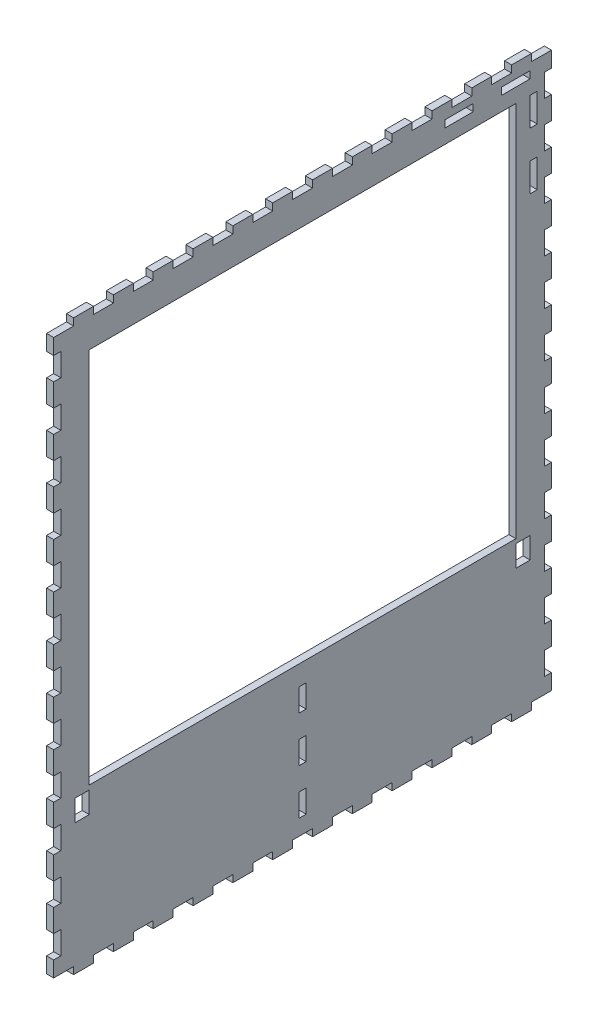
SolidWorks part; units mm, degrees
ref_plane "Plan de face" through (0, 0, 0) normal (0, 0, 1) x (1, 0, 0)
ref_plane "Plan de dessus" through (0, 0, 0) normal (0, 1, 0) x (1, 0, 0)
ref_plane "Plan de droite" through (0, 0, 0) normal (1, 0, 0) x (0, 0, -1)
sketch "Esquisse1" plane through (0, 0, 0) normal (1, 0, 0) x (0, 0, -1)
  line L1 (0, 0) -> (350, 0)
  line L2 (0, 0) -> (0, -400)
  line L3 (0, -400) -> (350, -400)
  line L4 (350, 0) -> (350, -400)
  dimension "D1" = 400
  dimension "D2" = 350
extrude "Boss.-Extru.1" add sketch "Esquisse1" along normal blind 5
sketch "Esquisse2" plane through (5, 0, 0) normal (1, 0, 0) x (0, 0, -1)
  line L0 (0, -400) -> (350, -400) construction
  line L1 (350, -400) -> (336, -400)
  line L2 (350, -400) -> (350, -395)
  line L3 (350, -395) -> (336, -395)
  line L4 (336, -400) -> (336, -395)
  dimension "D2" = 5
  dimension "D1" = 350
  dimension "D3" = 14
extrude "Enlèv. mat.-Extru.1" cut sketch "Esquisse2" against normal blind 5
ref_plane "Plan1" through (0, 0, -175) normal (0, 0, -1) x (-1, 0, 0)
ref_plane "Plan3" through (0, -200, 0) normal (0, -1, 0) x (-1, 0, 0)
pattern_linear "Répétition linéaire1" count 13 spacing 28 along (0, 0, 1) of "Enlèv. mat.-Extru.1"
mirror "Symétrie1" about plane through (0, -200, 0) normal (0, -1, 0) of "Répétition linéaire1", "Enlèv. mat.-Extru.1"
sketch "Esquisse3" plane through (5, 0, 0) normal (1, 0, 0) x (0, 0, -1)
  line L0 (350, -395) -> (350, -5) construction
  line L1 (350, -384) -> (345, -384)
  line L2 (350, -384) -> (350, -368)
  line L3 (350, -368) -> (345, -368)
  line L4 (345, -384) -> (345, -368)
  line L5 (336, -400) -> (336, 0) construction
  line L6 (322, -400) -> (336, -400) construction
  dimension "D1" = 400
  dimension "D2" = 16
  dimension "D3" = 16
  dimension "D4" = 5
extrude "Enlèv. mat.-Extru.2" cut sketch "Esquisse3" against normal blind 5
pattern_linear "Répétition linéaire2" count 12 spacing 32 along (0, 1, 0) of "Enlèv. mat.-Extru.2"
mirror "Symétrie2" about plane through (0, 0, -175) normal (0, 0, -1) of "Répétition linéaire2", "Enlèv. mat.-Extru.2"
sketch "Esquisse4" plane through (5, 0, 0) normal (1, 0, 0) x (0, 0, -1)
  line L0 (182, -400) -> (196, -400) construction
  line L1 (25, -25) -> (325, -25)
  line L2 (25, -25) -> (25, -290)
  line L3 (25, -290) -> (325, -290)
  line L4 (325, -25) -> (325, -290)
  line L5 (0, -128) -> (0, -144) construction
  line L6 (84, 0) -> (70, 0) construction
  line L7 (350, -48) -> (350, -32) construction
  dimension "D1" = 110
  dimension "D2" = 25
  dimension "D3" = 25
  dimension "D4" = 25
extrude "Enlèv. mat.-Extru.3" cut sketch "Esquisse4" against normal blind 5
sketch "Esquisse5" plane through (5, 0, 0) normal (1, 0, 0) x (0, 0, -1)
  line L0 (345, -304) -> (345, -320) construction
  line L1 (325, -293) -> (335, -293)
  line L2 (325, -293) -> (325, -308)
  line L3 (325, -308) -> (335, -308)
  line L4 (335, -293) -> (335, -308)
  line L5 (25, -290) -> (325, -290) construction
  dimension "D1" = 10
  dimension "D2" = 10
  dimension "D3" = 3
  dimension "D4" = 15
extrude "Enlèv. mat.-Extru.4" cut sketch "Esquisse5" against normal blind 5
mirror "Symétrie3" about plane through (0, 0, -175) normal (0, 0, -1) of "Enlèv. mat.-Extru.4"
sketch "Esquisse6" plane through (5, 0, 0) normal (1, 0, 0) x (0, 0, -1)
  line L1 (177.5, -384) -> (172.5, -384)
  line L2 (177.5, -384) -> (177.5, -368)
  line L3 (177.5, -368) -> (172.5, -368)
  line L4 (172.5, -384) -> (172.5, -368)
  line L5 (0, -352) -> (0, -368) construction
  line L7 (154, -400) -> (168, -400) construction
  line L8 (175, -368) -> (175, -384) construction
  line L9 (175, -2.75) -> (175, 2.75) construction
  dimension "D2" = 16
  dimension "D3" = 16
  dimension "D1" = 5
  dimension "D4" = 16
extrude "Enlèv. mat.-Extru.5" cut sketch "Esquisse6" against normal blind 5
pattern_linear "Répétition linéaire3" count 3 spacing 32 along (0, 1, 0) of "Enlèv. mat.-Extru.5"
sketch "Esquisse7" plane through (5, 0, 0) normal (1, 0, 0) x (0, 0, -1)
  line L0 (305, 45.3509) -> (305, -55) construction
  line L1 (275, -10) -> (295, -10)
  line L2 (275, -10) -> (275, -15)
  line L3 (275, -15) -> (295, -15)
  line L4 (295, -10) -> (295, -15)
  line L5 (248.1608, -55) -> (383.9975, -55) construction
  line L6 (322, -5) -> (308, -5) construction
  line L7 (345, -16) -> (345, -32) construction
  line L8 (294, -5) -> (280, -5) construction
  line L9 (315, -10) -> (315, -15)
  line L10 (335, -15) -> (315, -15)
  line L11 (335, -10) -> (335, -15)
  line L12 (335, -10) -> (315, -10)
  line L13 (340, -85) -> (340, -65)
  line L14 (335, -25) -> (340, -25)
  line L15 (335, -25) -> (335, -45)
  line L16 (335, -45) -> (340, -45)
  line L17 (340, -25) -> (340, -45)
  line L18 (335, -85) -> (340, -85)
  line L19 (335, -85) -> (335, -65)
  line L20 (335, -65) -> (340, -65)
  dimension "D4" = 5
  dimension "D1" = 50
  dimension "D2" = 40
  dimension "D3" = 20
  dimension "D5" = 10
  dimension "D6" = 5
  dimension "D7" = 20
  dimension "D8" = 5
  dimension "D9" = 10
  dimension "D10" = 5
extrude "Enlèv. mat.-Extru.6" cut sketch "Esquisse7" against normal blind 10
equation "\"D3@Esquisse2\"=\"D1@Esquisse2\"/25"
equation "\"D2@Esquisse3\"=\"D1@Esquisse3\"/25"
equation "\"D3@Esquisse3\"=\"D2@Esquisse3\""
equation "\"D3@Esquisse4\"=\"D2@Esquisse4\""
equation "\"D4@Esquisse4\"=\"D2@Esquisse4\""
equation "\"D2@Esquisse6\"=\"D3@Esquisse6\""
equation "\"D4@Esquisse6\"=\"D2@Esquisse6\""
equation "\"D5@Esquisse7\"=\"D3@Esquisse7\"/2"
equation "\"D9@Esquisse7\"=\"D7@Esquisse7\"/2"
